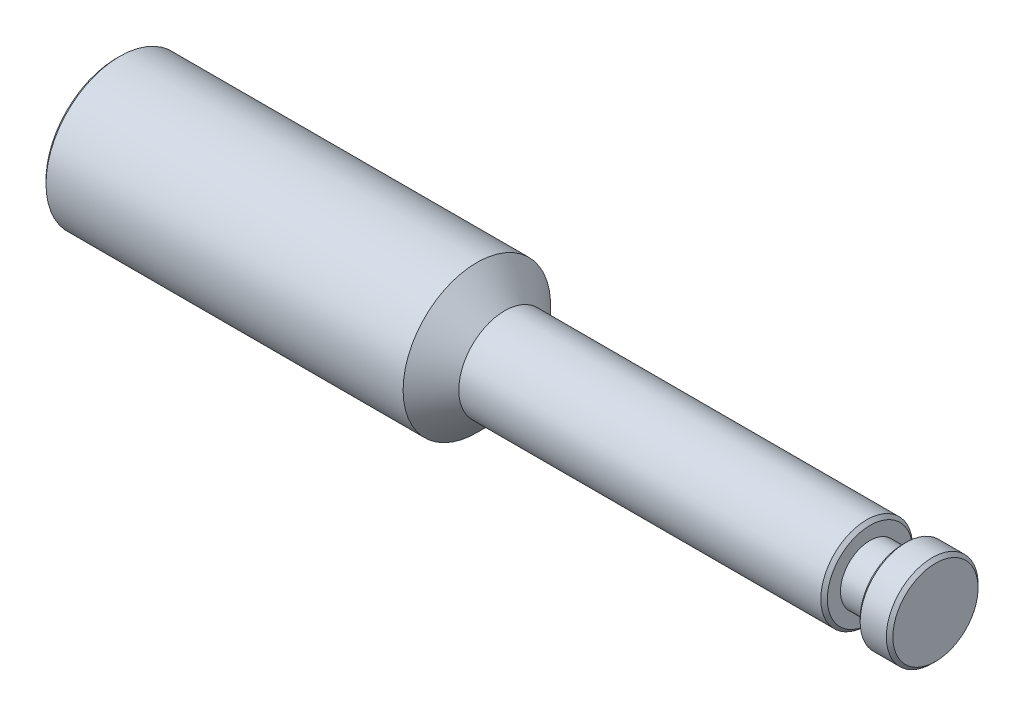
SolidWorks part; units mm, degrees
ref_plane "Front Plane" through (0, 0, 0) normal (0, 0, 1) x (1, 0, 0)
ref_plane "Top Plane" through (0, 0, 0) normal (0, 1, 0) x (1, 0, 0)
ref_plane "Right Plane" through (0, 0, 0) normal (1, 0, 0) x (0, 0, -1)
sketch "Sketch1" plane through (0, 0, 0) normal (0, 0, 1) x (1, 0, 0)
  line L0 (0, 0) -> (287.2671, 0) construction
  line L1 (0, 0) -> (0, 22.5)
  line L2 (0, 22.5) -> (110, 22.5)
  line L3 (110, 22.5) -> (118.5, 14)
  line L4 (118.5, 14) -> (250, 14)
  line L5 (250, 14) -> (250, 0)
  line L6 (250, 0) -> (0, 0)
  dimension "D1" = 250
  dimension "D2" = 110
  dimension "D3" = 14
  dimension "D4" = 22.5
  dimension "D5" = 135
revolve "Revolve1" add sketch "Sketch1" angle 360 about L0
sketch "Sketch2" plane through (0, 0, 0) normal (0, 0, 1) x (1, 0, 0)
  line L0 (0, 0) -> (250, 0) construction
  line L1 (250, -14) -> (250, 14) construction
  line L2 (250, 14) -> (118.5, 14) construction
  line L3 (230, 14) -> (240, 14)
  line L4 (230, 14) -> (230, 9)
  line L5 (230, 9) -> (240, 9)
  line L6 (240, 14) -> (240, 9)
  line L7 (0, 22.5) -> (0, -22.5) construction
  dimension "D1" = 10
  dimension "D2" = 9
  dimension "D3" = 230
revolve "Cut-Revolve1" cut sketch "Sketch2" angle 360 about L0
chamfer "Chamfer1" distance 1 4 edges at (250, 0, 14) (240, -14, 0) (230, -14, 0) (0, 0, 22.5)
